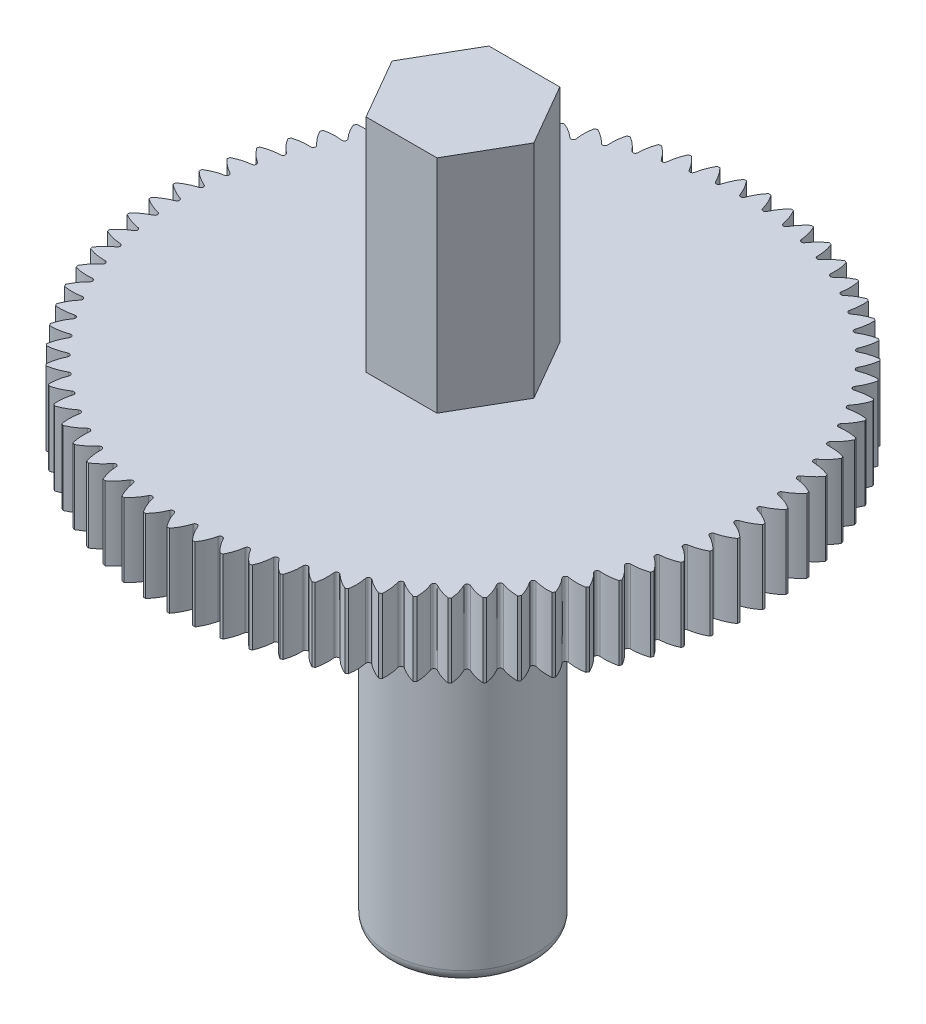
SolidWorks part; units mm, degrees
ref_plane "Front Plane" through (0, 0, 0) normal (0, 0, 1) x (1, 0, 0)
ref_plane "Top Plane" through (0, 0, 0) normal (0, 1, 0) x (1, 0, 0)
ref_plane "Right Plane" through (0, 0, 0) normal (1, 0, 0) x (0, 0, -1)
sketch "Sketch1" plane through (0, 0, 0) normal (0, 0, 1) x (1, 0, 0)
  line L0 (0, 0) -> (0, 29)
  line L1 (0, 0) -> (3, 0)
  line L2 (3, 0) -> (3, 17)
  line L3 (3, 17) -> (12, 17)
  line L4 (12, 17) -> (12, 20)
  line L5 (12, 20) -> (3, 20)
  line L6 (3, 20) -> (3, 29)
  line L7 (3, 29) -> (0, 29)
  dimension "D1" = 29
  dimension "D2" = 3
  dimension "D3" = 17
  dimension "D4" = 9
  dimension "D5" = 9
  dimension "D6" = 3
revolve "Revolve1" add sketch "Sketch1" angle 360 about L0
fillet "Fillet1" radius 0.5 1 edges at (0, 0, -3)
sketch "Sketch2" plane through (0, 29, 0) normal (0, 1, 0) x (1, 0, 0)
  line L1 (1.4434, 2.5) -> (-1.4434, 2.5)
  line L2 (-1.4434, 2.5) -> (-2.8868, 0)
  line L3 (-2.8868, 0) -> (-1.4434, -2.5)
  line L4 (-1.4434, -2.5) -> (1.4434, -2.5)
  line L5 (1.4434, -2.5) -> (2.8868, 0)
  line L6 (2.8868, 0) -> (1.4434, 2.5)
  circle A0 centre (0, 0) radius 2.5 construction
  dimension "D1" = 5
extrude "Cut-Extrude1" cut sketch "Sketch2" against normal blind 9 flip side to cut
sketch "Sketch3" plane through (0, 20, 0) normal (0, 1, 0) x (1, 0, 0)
  line L0 (0, 0) -> (0, 14.0435) construction
  circle A0 centre (0, 0) radius 12 construction
  circle A1 centre (0, 0) radius 12
  arc A2 (-0.45, 11.9916) -> (-0.0942, 11.3714) centre (-1.979, 10.7023) cw
  arc A3 (0.0942, 11.3714) -> (0.45, 11.9916) centre (1.979, 10.7023) cw
  arc A4 (0.0942, 11.3714) -> (-0.0942, 11.3714) centre (0, 11.4049) cw
  point P13 (0, 10.9916)
  circle M2 centre (0, 0) radius 12
  dimension "D1" = 0.9
  dimension "D3" = 2
  dimension "D4" = 2
  dimension "D5" = 0.1
  dimension "D2" = 1
extrude "Cut-Extrude2" cut sketch "Sketch3" against normal blind 9 contours A4 L0 A2 M2 | L0 A4 A3 A1
pattern_circular "CirPattern1" count 75 over 360 about axis through (0, 0, 0) along (0, 1, 0) of "Cut-Extrude2"
